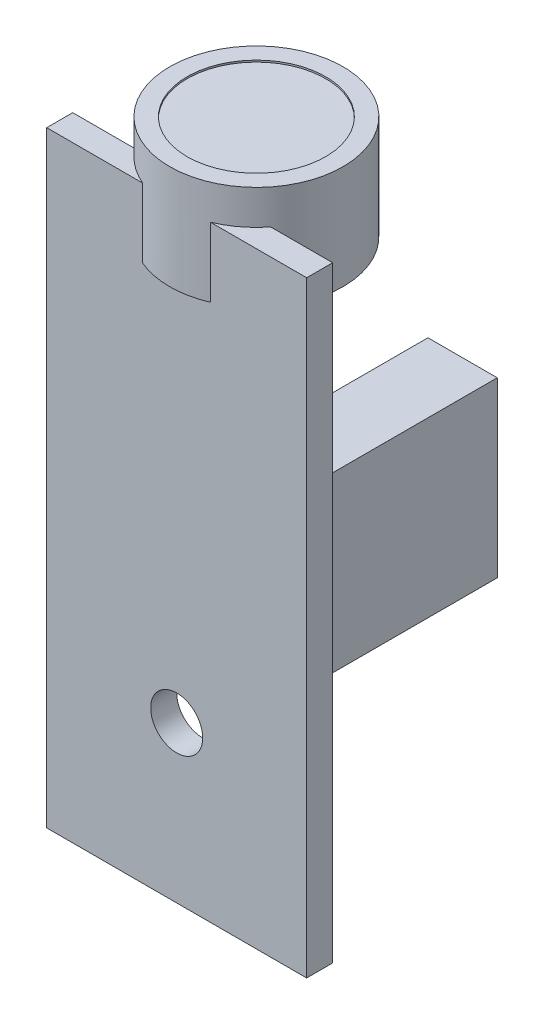
SolidWorks part; units mm, degrees
ref_plane "Front Plane" through (0, 0, 0) normal (0, 0, 1) x (1, 0, 0)
ref_plane "Top Plane" through (0, 0, 0) normal (0, 1, 0) x (1, 0, 0)
ref_plane "Right Plane" through (0, 0, 0) normal (1, 0, 0) x (0, 0, -1)
sketch "Sketch1" plane through (0, 0, 0) normal (0, 0, 1) x (1, 0, 0)
  line L1 (212.6352, 134.3941) -> (227.6352, 134.3941)
  line L2 (212.6352, 134.3941) -> (212.6352, 169.3941)
  line L3 (212.6352, 169.3941) -> (227.6352, 169.3941)
  line L4 (227.6352, 134.3941) -> (227.6352, 169.3941)
  circle A0 centre (220.1352, 143.3941) radius 1.5
extrude "Boss-Extrude1" add sketch "Sketch1" along normal blind 1.5
sketch "Sketch2" plane through (0, 169.3941, 0) normal (0, 1, 0) x (1, 0, 0)
  circle A0 centre (220.1352, 3.1) radius 5
extrude "Boss-Extrude2" add sketch "Sketch2" along normal blind 2 and the other way blind 4
sketch "Sketch3" plane through (0, 171.3941, 0) normal (0, 1, 0) x (1, 0, 0)
  circle A2 centre (220.1352, 3.1) radius 4
  circle A3 centre (220.1352, 3.1) radius 4
  dimension "D1" = 1
extrude "Cut-Extrude1" cut sketch "Sketch3" against normal blind 0.1
sketch "Sketch4" plane through (0, 0, 0) normal (0, 0, -1) x (-1, 0, 0)
  line L1 (-227.1352, 158.3941) -> (-223.1352, 158.3941)
  line L2 (-227.1352, 158.3941) -> (-227.1352, 148.3941)
  line L3 (-227.1352, 148.3941) -> (-223.1352, 148.3941)
  line L4 (-223.1352, 158.3941) -> (-223.1352, 148.3941)
extrude "Boss-Extrude3" add sketch "Sketch4" along normal blind 10
